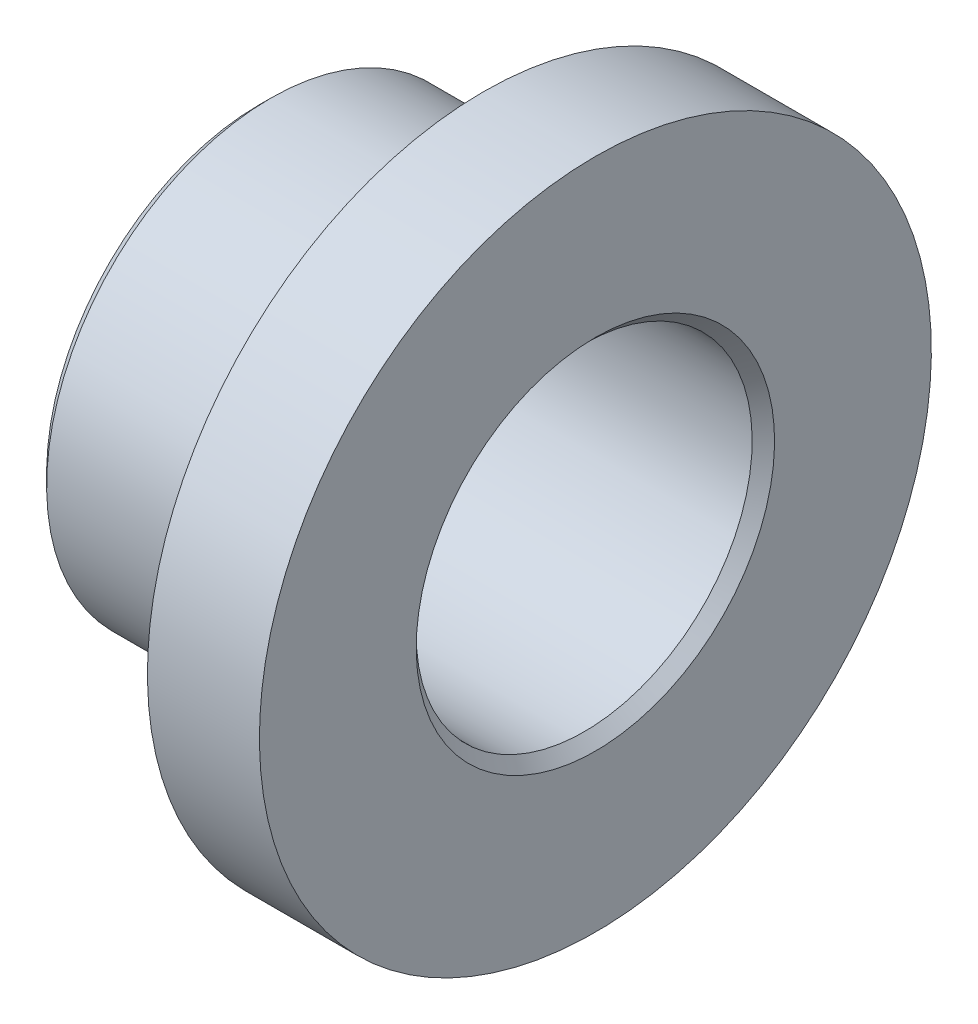
SolidWorks part; units mm, degrees
material "Acier non allié"
ref_plane "Plan de face" through (0, 0, 0) normal (0, 0, 1) x (1, 0, 0)
ref_plane "Plan de dessus" through (0, 0, 0) normal (0, 1, 0) x (1, 0, 0)
ref_plane "Plan de droite" through (0, 0, 0) normal (1, 0, 0) x (0, 0, -1)
sketch "Esquisse1" plane through (0, 0, 0) normal (0, 0, 1) x (1, 0, 0)
  line L0 (0, 0) -> (-45, 0) construction
  line L2 (0, 30) -> (-40, 30)
  line L3 (0, 30) -> (0, 40)
  line L4 (0, 40) -> (-40, 40)
  line L5 (-40, 30) -> (-40, 40)
  line L6 (0, 30) -> (20, 30)
  line L7 (0, 30) -> (0, 60)
  line L8 (0, 60) -> (20, 60)
  line L9 (20, 30) -> (20, 60)
  dimension "D1" = 40
  dimension "D2" = 20
  dimension "D3" = 120
  dimension "D4" = 60
  dimension "D5" = 80
revolve "Révolution1" add sketch "Esquisse1" angle 360 about L0
chamfer "Chanfrein1" distance 2 angle 45 3 edges at (-40, 30, 0) (20, 30, 0) (-40, 40, 0)
